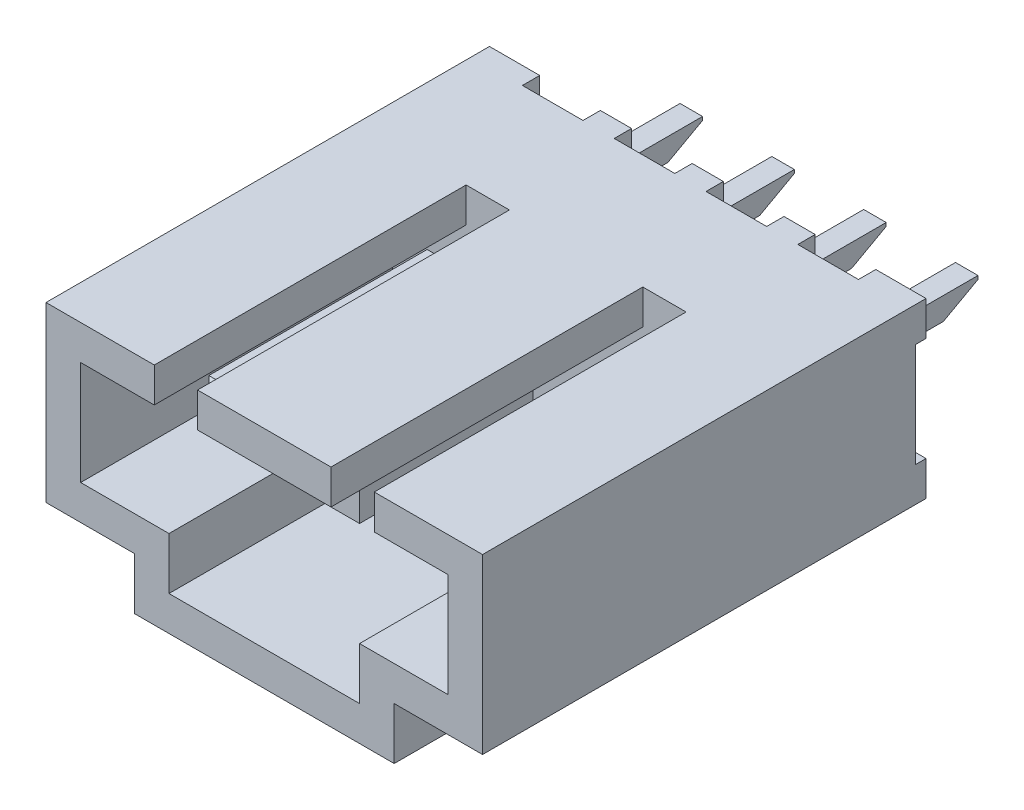
SolidWorks part; units mm, degrees
ref_plane "Front Plane" through (0, 0, 0) normal (0, 0, 1) x (1, 0, 0)
ref_plane "Top Plane" through (0, 0, 0) normal (0, 1, 0) x (1, 0, 0)
ref_plane "Right Plane" through (0, 0, 0) normal (1, 0, 0) x (0, 0, -1)
sketch "Sketch1" plane through (0, 0, 0) normal (0, 0, 1) x (1, 0, 0)
  line L0 (0, 0) -> (6.3, 0)
  line L1 (6.3, 0) -> (6.3, -5)
  line L2 (6.3, -5) -> (3.75, -5)
  line L3 (3.75, -5) -> (3.75, -6.5)
  line L4 (3.75, -6.5) -> (0, -6.5)
  line L5 (0, 0) -> (0, -6.5) construction
  line L16 (-3.75, -6.5) -> (0, -6.5)
  line L17 (-3.75, -5) -> (-3.75, -6.5)
  line L18 (-6.3, -5) -> (-3.75, -5)
  line L19 (-6.3, 0) -> (-6.3, -5)
  line L20 (0, 0) -> (-6.3, 0)
  dimension "D1" = 6.5
  dimension "D2" = 5
  dimension "D3" = 6.3
  dimension "D4" = 3.75
extrude "Boss-Extrude1" add sketch "Sketch1" along normal blind 12.8
sketch "Sketch4" plane through (0, 0, 12.8) normal (0, 0, 1) x (1, 0, 0)
  line L8 (-2.75, -4) -> (-1.25, -4)
  line L9 (-1.25, -4) -> (-1.25, -5)
  line L10 (-1.25, -5) -> (-2.75, -5)
  line L11 (2.75, -4) -> (1.25, -4)
  line L12 (1.25, -4) -> (1.25, -5)
  line L13 (1.25, -5) -> (2.75, -5)
  line L14 (0, 0) -> (0, -1) construction
  line L15 (6.3, 0) -> (-6.3, 0) construction
  line L16 (5.3, -4) -> (5.3, -1)
  line L17 (5.3, -1) -> (-5.3, -1)
  line L18 (-5.3, -1) -> (-5.3, -4)
  line L19 (-5.3, -4) -> (-2.75, -4)
  line L20 (-2.75, -4) -> (-2.75, -5.5)
  line L21 (-2.75, -5.5) -> (2.75, -5.5)
  line L22 (2.75, -5.5) -> (2.75, -4)
  line L23 (2.75, -4) -> (5.3, -4)
  line L24 (5.3, -4) -> (5.3, -1)
  line L25 (5.3, -1) -> (3.175, -1)
  line L26 (-5.3, -1) -> (-5.3, -4)
  line L27 (-5.3, -4) -> (-2.75, -4)
  line L28 (-2.75, -5) -> (-2.75, -5.5)
  line L29 (-2.75, -5.5) -> (2.75, -5.5)
  line L30 (2.75, -5.5) -> (2.75, -5)
  line L31 (2.75, -4) -> (5.3, -4)
  line L32 (1.925, 0) -> (3.175, 0)
  line L33 (1.925, 0) -> (1.925, -1)
  line L35 (3.175, 0) -> (3.175, -1)
  line L36 (1.925, -1) -> (-1.925, -1)
  line L37 (-3.175, 0) -> (-3.175, -1)
  line L38 (-1.925, 0) -> (-3.175, 0)
  line L39 (-1.925, 0) -> (-1.925, -1)
  line L40 (-3.175, -1) -> (-5.3, -1)
  dimension "D2" = 2.5
  dimension "D3" = 1
  dimension "D4" = 1.25
  dimension "D5" = 1.925
  dimension "D1" = 1
extrude "Cut-Extrude2" cut sketch "Sketch4" against normal blind 9
sketch "Sketch5" plane through (0, 0, 12.8) normal (0, 0, 1) x (1, 0, 0)
  line L1 (-1.25, -4) -> (-2.75, -4)
  line L2 (-1.25, -4) -> (-1.25, -5)
  line L3 (-1.25, -5) -> (-2.75, -5)
  line L4 (-2.75, -4) -> (-2.75, -5)
  line L5 (1.25, -4) -> (2.75, -4)
  line L6 (1.25, -4) -> (1.25, -5)
  line L7 (1.25, -5) -> (2.75, -5)
  line L8 (2.75, -4) -> (2.75, -5)
extrude "Cut-Extrude3" cut sketch "Sketch5" against normal blind 4
ref_plane "Plane1" through (0, 0, 10.3) normal (0, 0, 1) x (1, 0, 0)
sketch "Sketch6" plane through (0, 0, 10.3) normal (0, 0, 1) x (1, 0, 0)
  line L0 (0, -1) -> (0, -5.5) construction
  line L1 (1.925, -1) -> (-1.925, -1) construction
  line L2 (-2.75, -5.5) -> (2.75, -5.5) construction
  line L3 (4.3, -2.5) -> (5.3, -2.5) construction
  line L4 (1, -2.175) -> (1.65, -2.175)
  line L5 (1, -2.175) -> (1, -2.825)
  line L6 (1, -2.825) -> (1.65, -2.825)
  line L7 (1.65, -2.175) -> (1.65, -2.825)
  line L8 (3.65, -2.175) -> (4.3, -2.175)
  line L9 (3.65, -2.175) -> (3.65, -2.825)
  line L10 (3.65, -2.825) -> (4.3, -2.825)
  line L11 (4.3, -2.175) -> (4.3, -2.825)
  line L12 (5.3, -4) -> (5.3, -1) construction
  line L13 (-3.65, -2.825) -> (-4.3, -2.825)
  line L14 (-1, -2.825) -> (-1.65, -2.825)
  line L15 (-4.3, -2.175) -> (-4.3, -2.825)
  line L16 (-3.65, -2.175) -> (-3.65, -2.825)
  line L17 (-3.65, -2.175) -> (-4.3, -2.175)
  line L18 (-1.65, -2.175) -> (-1.65, -2.825)
  line L19 (-1, -2.175) -> (-1, -2.825)
  line L20 (-1, -2.175) -> (-1.65, -2.175)
  dimension "D1" = 0.65
  dimension "D2" = 1
  dimension "D3" = 2
extrude "Boss-Extrude3" add sketch "Sketch6" against normal blind 13.8 separate body
sketch "Sketch7" plane through (0, 0, 0) normal (0, 1, 0) x (1, 0, 0)
  line L0 (6.3, 0) -> (-6.3, 0) construction
  line L1 (-4.85, 0) -> (-3.1, 0)
  line L2 (-4.85, 0) -> (-4.85, -0.5)
  line L3 (-4.85, -0.5) -> (-3.1, -0.5)
  line L4 (-3.1, 0) -> (-3.1, -0.5)
  line L6 (-2.2, 0) -> (-0.45, 0)
  line L7 (-2.2, 0) -> (-2.2, -0.5)
  line L8 (-2.2, -0.5) -> (-0.45, -0.5)
  line L9 (-0.45, 0) -> (-0.45, -0.5)
  line L10 (0.45, 0) -> (2.2, 0)
  line L11 (0.45, 0) -> (0.45, -0.5)
  line L12 (0.45, -0.5) -> (2.2, -0.5)
  line L13 (2.2, 0) -> (2.2, -0.5)
  line L14 (3.1, 0) -> (4.85, 0)
  line L15 (3.1, 0) -> (3.1, -0.5)
  line L16 (3.1, -0.5) -> (4.85, -0.5)
  line L17 (4.85, 0) -> (4.85, -0.5)
  line L18 (-3.975, 3.5) -> (-3.975, 0) construction
  line L19 (-3.65, 3.5) -> (-4.3, 3.5) construction
  line L20 (-1.325, 3.5) -> (-1.325, 0) construction
  line L21 (-1, 3.5) -> (-1.65, 3.5) construction
  line L22 (1.325, 3.5) -> (1.325, 0) construction
  line L23 (1.65, 3.5) -> (1, 3.5) construction
  line L24 (3.975, 3.5) -> (3.975, 0) construction
  line L25 (4.3, 3.5) -> (3.65, 3.5) construction
  dimension "D1" = 0.5
  dimension "D2" = 1.75
extrude "Cut-Extrude5" cut sketch "Sketch7" against normal through all
sketch "Sketch8" plane through (-6.3, 0, 0) normal (-1, 0, 0) x (0, 0, 1)
  line L0 (0, 0) -> (0, -5) construction
  line L1 (0, -1) -> (0.3, -1)
  line L2 (0, -1) -> (0, -4)
  line L3 (0, -4) -> (0.3, -4)
  line L4 (0.3, -1) -> (0.3, -4)
  line L5 (-3.5, -2.5) -> (0, -2.5) construction
  line L6 (-3.5, -2.175) -> (-3.5, -2.825) construction
  dimension "D1" = 3
  dimension "D2" = 0.3
extrude "Cut-Extrude6" cut sketch "Sketch8" against normal through all
sketch "Sketch9" plane through (-4.3, 0, 0) normal (-1, 0, 0) x (0, 0, 1)
  line L0 (-3.5, -2.275) -> (-2.5, -2.825)
  line L1 (-3.5, -2.175) -> (-3.5, -2.825) construction
  line L2 (-3.5, -2.825) -> (10.3, -2.825) construction
  line L3 (-2.5, -2.825) -> (-3.5, -2.825)
  line L4 (-3.5, -2.825) -> (-3.5, -2.275)
  dimension "D1" = 0.55
  dimension "D2" = 1
extrude "Cut-Extrude7" cut sketch "Sketch9" against normal through all
chamfer "Chamfer1" distance 0.2 angle 45 4 edges at (-1.325, -2.825, 10.3) (-1.65, -2.5, 10.3) (-1.325, -2.175, 10.3) (-1, -2.5, 10.3)
chamfer "Chamfer2" distance 0.2 angle 45 4 edges at (-3.975, -2.825, 10.3) (-4.3, -2.5, 10.3) (-3.975, -2.175, 10.3) (-3.65, -2.5, 10.3)
chamfer "Chamfer3" distance 0.2 angle 45 4 edges at (1.325, -2.175, 10.3) (1.65, -2.5, 10.3) (1.325, -2.825, 10.3) (1, -2.5, 10.3)
chamfer "Chamfer4" distance 0.2 angle 45 4 edges at (3.975, -2.175, 10.3) (4.3, -2.5, 10.3) (3.975, -2.825, 10.3) (3.65, -2.5, 10.3)
